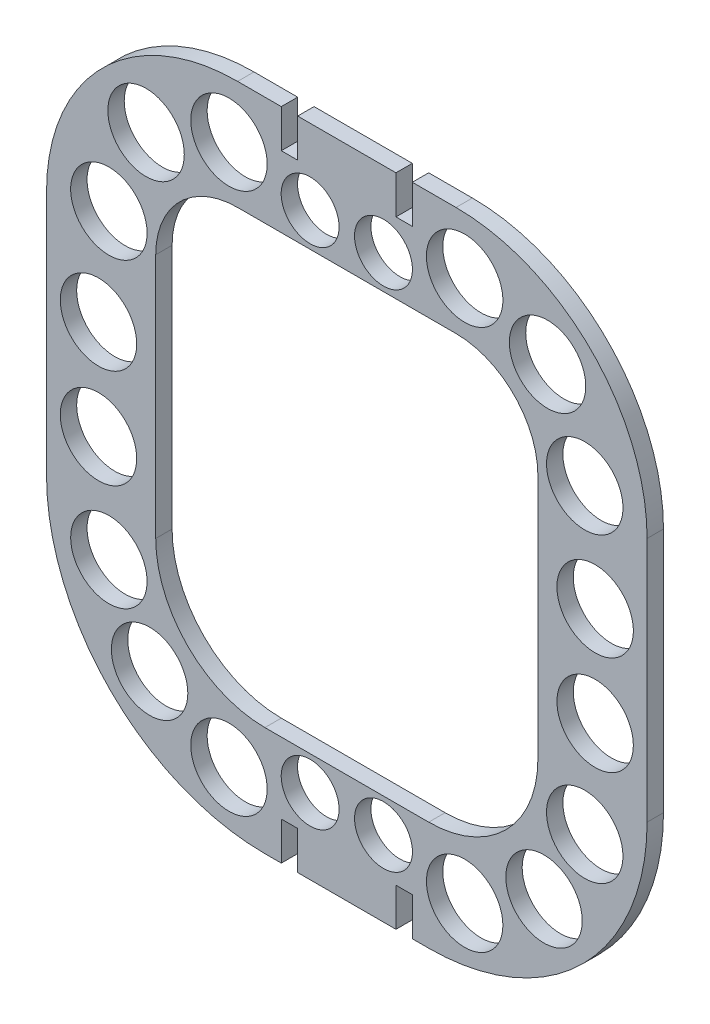
SolidWorks part; units mm, degrees
ref_plane "Front Plane" through (0, 0, 0) normal (0, 0, 1) x (1, 0, 0)
ref_plane "Top Plane" through (0, 0, 0) normal (0, 1, 0) x (1, 0, 0)
ref_plane "Right Plane" through (0, 0, 0) normal (1, 0, 0) x (0, 0, -1)
sketch "Sketch1" plane through (0, 0, 0) normal (0, 0, 1) x (1, 0, 0)
  line L0 (0, 52) -> (0, -68) construction
  line L1 (-55, 52) -> (55, 52) construction
  line L2 (-55, 52) -> (-55, -68) construction
  line L3 (-55, -68) -> (55, -68) construction
  line L4 (55, 52) -> (55, -68) construction
  line L5 (-20, 52) -> (20, 52)
  line L6 (-15, -68) -> (15, -68) construction
  line L7 (-55, 17) -> (55, 17) construction
  line L8 (-55, 17) -> (-55, -28)
  line L9 (-55, -28) -> (55, -28) construction
  line L10 (55, 17) -> (55, -28)
  line L11 (-0.5, -68) -> (0.5, -68) construction
  line L12 (-15, -68) -> (-0.5, -68)
  line L13 (0.5, -68) -> (15, -68)
  line L14 (-0.5, -68) -> (0.5, -68)
  line L15 (-20, 32) -> (20, 32)
  line L16 (35, 17) -> (35, -28)
  line L17 (0.5, -48) -> (15, -48)
  line L18 (-0.5, -48) -> (0.5, -48)
  line L19 (-15, -48) -> (-0.5, -48)
  line L20 (-35, 17) -> (-35, -28)
  arc A0 (-55, 17) -> (-20, 52) centre (-20, 17) cw
  arc A1 (20, 52) -> (55, 17) centre (20, 17) cw
  arc A2 (-55, -28) -> (-15, -68) centre (-15, -28) ccw
  arc A3 (15, -68) -> (55, -28) centre (15, -28) ccw
  arc A4 (-35, 17) -> (-20, 32) centre (-20, 17) cw
  arc A5 (20, 32) -> (35, 17) centre (20, 17) cw
  arc A6 (15, -48) -> (35, -28) centre (15, -28) ccw
  arc A7 (-35, -28) -> (-15, -48) centre (-15, -28) ccw
  point P9 (0, 52)
  point P18 (0, -68)
  point P22 (0, -68)
  dimension "D3" = 40
  dimension "D4" = 35
  dimension "D1" = 120
  dimension "D2" = 110
  dimension "D5" = 1
  dimension "D6" = 52
  dimension "D7" = 20
extrude "Boss-Extrude1" add sketch "Sketch1" along normal blind 3
sketch "Sketch2" plane through (0, 0, 3) normal (0, 0, 1) x (1, 0, 0)
  line L0 (20, 52) -> (-20, 52) construction
  line L1 (-12, 52) -> (-9, 52)
  line L2 (-12, 52) -> (-12, 45)
  line L3 (-12, 45) -> (-9, 45)
  line L4 (-9, 52) -> (-9, 45)
  line L5 (-15, -68) -> (15, -68) construction
  line L6 (-9, -68) -> (-12, -68)
  line L7 (-9, -68) -> (-9, -61)
  line L8 (-9, -61) -> (-12, -61)
  line L9 (-12, -68) -> (-12, -61)
  line L10 (0, -1.65) -> (0, 1.65) construction
  line L11 (9, -61) -> (12, -61)
  line L12 (12, -68) -> (12, -61)
  line L13 (9, -68) -> (12, -68)
  line L14 (9, -68) -> (9, -61)
  line L15 (12, 45) -> (9, 45)
  line L16 (9, 52) -> (9, 45)
  line L17 (12, 52) -> (9, 52)
  line L18 (12, 52) -> (12, 45)
  dimension "D1" = 3
  dimension "D2" = 7
  dimension "D3" = 9
  dimension "D4" = 9
extrude "Cut-Extrude1" cut sketch "Sketch2" against normal blind 10
sketch "Sketch3" plane through (0, 0, 3) normal (0, 0, 1) x (1, 0, 0)
  line L0 (0, 0) -> (0, 7.3982) construction
  line L1 (-35, -8) -> (35, -8) construction
  line L4 (0, -16) -> (0, -23.3982) construction
  line L5 (0, -8) -> (0, 32) construction
  line L6 (20, 32) -> (-20, 32) construction
  line L7 (0, -8) -> (0, -48) construction
  line L8 (-15, -48) -> (15, -48) construction
  circle A0 centre (-45.4811, 1.0902) radius 7
  circle A1 centre (-43.5787, 19.6394) radius 7
  circle A2 centre (-36.7686, 35.5078) radius 7
  circle A3 centre (-21.5812, 41.572) radius 7
  circle A4 centre (-6.7181, 38.1886) radius 5.3029
  circle A8 centre (-6.7181, -54.1886) radius 5.3029
  circle A9 centre (-21.5812, -57.572) radius 7
  circle A11 centre (-43.5787, -35.6394) radius 7
  circle A12 centre (-45.4811, -17.0902) radius 7
  circle A13 centre (45.4811, -17.0902) radius 7
  circle A14 centre (43.5787, -35.6394) radius 7
  circle A16 centre (21.5812, -57.572) radius 7
  circle A17 centre (6.7181, -54.1886) radius 5.3029
  circle A18 centre (6.7181, 38.1886) radius 5.3029
  circle A19 centre (21.5812, 41.572) radius 7
  circle A20 centre (36.7686, 35.5078) radius 7
  circle A21 centre (43.5787, 19.6394) radius 7
  circle A22 centre (45.4811, 1.0902) radius 7
  circle A23 centre (-36.1201, -49.6242) radius 7
  circle A25 centre (36.1201, -49.6242) radius 7
  dimension "D1" = 14
  dimension "D2" = 14
extrude "Cut-Extrude2" cut sketch "Sketch3" against normal blind 10
